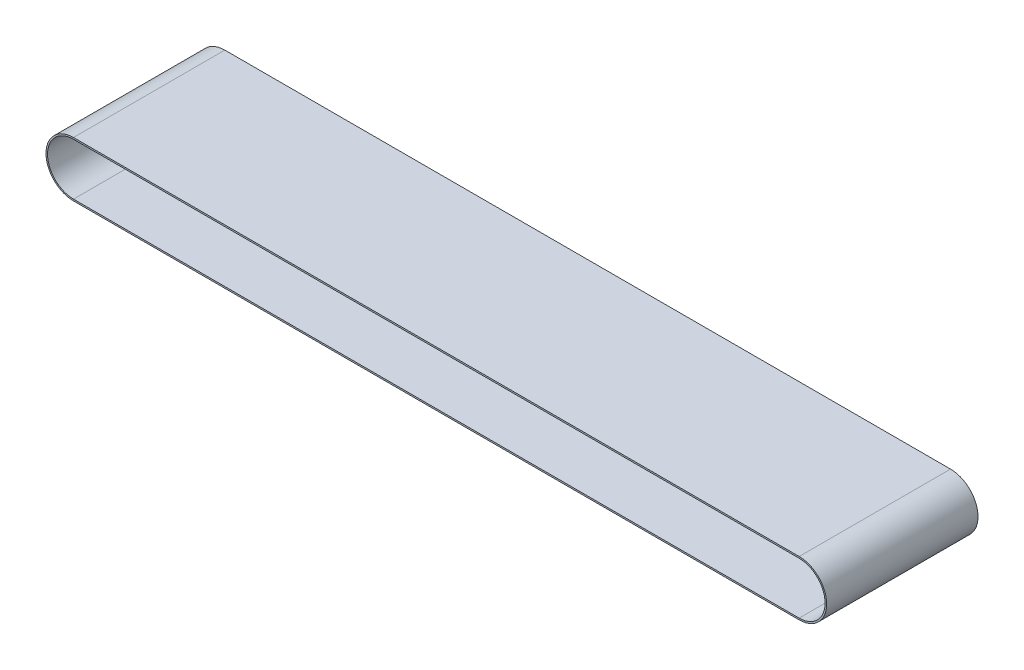
SolidWorks part; units mm, degrees
ref_plane "Front Plane" through (0, 0, 0) normal (0, 0, 1) x (1, 0, 0)
ref_plane "Top Plane" through (0, 0, 0) normal (0, 1, 0) x (1, 0, 0)
ref_plane "Right Plane" through (0, 0, 0) normal (1, 0, 0) x (0, 0, -1)
sketch "Sketch1" plane through (0, 0, 0) normal (0, 0, 1) x (1, 0, 0)
  line L0 (0, 0) -> (700, 0) construction
  line L1 (0, 26.5) -> (700, 26.5)
  line L2 (0, -26.5) -> (700, -26.5)
  line L3 (0, 0) -> (700, 0) construction
  line L4 (0, 25) -> (700, 25)
  line L5 (0, -25) -> (700, -25)
  arc A0 (0, 26.5) -> (0, -26.5) centre (0, 0) ccw
  arc A1 (700, -26.5) -> (700, 26.5) centre (700, 0) ccw
  arc A2 (0, 25) -> (0, -25) centre (0, 0) ccw
  arc A3 (700, -25) -> (700, 25) centre (700, 0) ccw
  point P3 (350, 0)
  point P10 (350, 0)
  dimension "D1" = 700
  dimension "D2" = 53
  dimension "D3" = 700
  dimension "D4" = 50
extrude "Boss-Extrude1" add sketch "Sketch1" along normal mid plane 146
